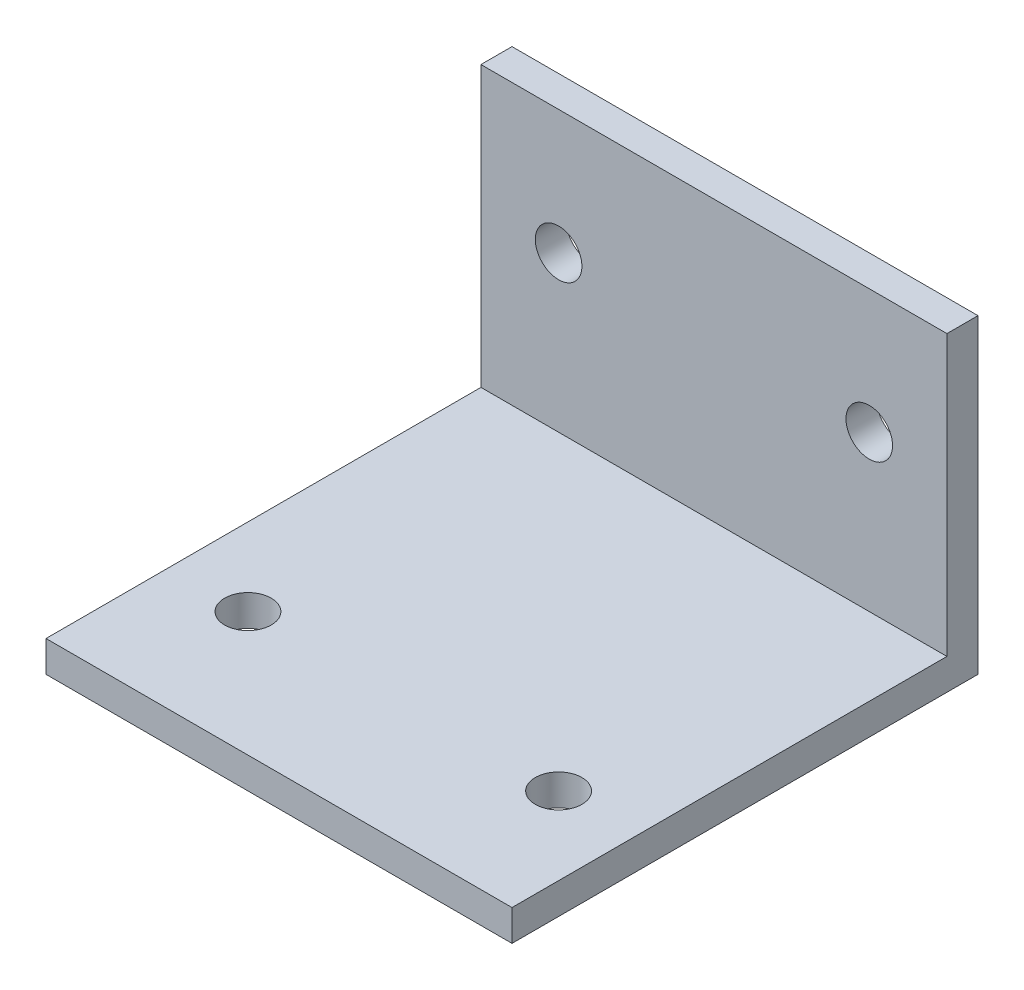
SolidWorks part; units mm, degrees
material "AISI 304"
ref_plane "前视基准面" through (0, 0, 0) normal (0, 0, 1) x (1, 0, 0)
ref_plane "上视基准面" through (0, 0, 0) normal (0, 1, 0) x (1, 0, 0)
ref_plane "右视基准面" through (0, 0, 0) normal (1, 0, 0) x (0, 0, -1)
sketch "草图1" plane through (0, 0, 0) normal (0, 0, 1) x (1, 0, 0)
  line L1 (-15, 19) -> (15, 19)
  line L2 (-15, 19) -> (-15, -19)
  line L3 (-15, -19) -> (15, -19)
  line L4 (15, 19) -> (15, -19)
  line L5 (-15, 19) -> (15, -19) construction
  line L6 (-15, -19) -> (15, 19) construction
  point P0 (0, 0)
  dimension "D1" = 30
  dimension "D2" = 38
extrude "凸台-拉伸1" add sketch "草图1" along normal blind 3
sketch "草图2" plane through (0, 0, 3) normal (0, 0, 1) x (1, 0, 0)
  line L0 (15, -19) -> (15, 19) construction
  line L1 (-15, -19) -> (15, -19)
  line L2 (-15, -19) -> (-15, -16)
  line L3 (-15, -16) -> (15, -16)
  line L4 (15, -19) -> (15, -16)
  dimension "D1" = 3
extrude "凸台-拉伸2" add sketch "草图2" along normal blind 35
sketch "草图3" plane through (0, 0, 3) normal (0, 0, 1) x (1, 0, 0)
  line L0 (15, -16) -> (15, 19) construction
  line L1 (-15, 19) -> (-15, -16) construction
  line L2 (15, 19) -> (-15, 19) construction
  circle A0 centre (-10, -6) radius 1.5
  circle A1 centre (10, -6) radius 1.5
  dimension "D1" = 3
  dimension "D2" = 3
  dimension "D3" = 5
  dimension "D4" = 5
  dimension "D5" = 25
  dimension "D6" = 25
extrude "切除-拉伸1" cut sketch "草图3" against normal blind 35
sketch "草图4" plane through (0, -16, 0) normal (0, 1, 0) x (1, 0, 0)
  line L1 (15, -38) -> (15, -3) construction
  line L2 (-15, -38) -> (-15, -3) construction
  line L3 (15, -38) -> (-15, -38) construction
  circle A0 centre (-10, -23) radius 1.5
  circle A1 centre (10, -23) radius 1.5
  dimension "D1" = 3
  dimension "D2" = 3
  dimension "D3" = 5
  dimension "D4" = 5
  dimension "D5" = 15
extrude "切除-拉伸2" cut sketch "草图4" against normal blind 35
sketch "草图5" plane through (0, -19, 0) normal (0, -1, 0) x (1, 0, 0)
  line L1 (-41.1883, 49.4744) -> (47.4485, 49.4744)
  line L2 (-41.1883, 49.4744) -> (-41.1883, -14.1195)
  line L3 (-41.1883, -14.1195) -> (47.4485, -14.1195)
  line L4 (47.4485, 49.4744) -> (47.4485, -14.1195)
extrude "切除-拉伸3" cut sketch "草图5" against normal blind 1
sketch "草图6" plane through (0, 0, 0) normal (0, 0, -1) x (-1, 0, 0)
  line L1 (25.7068, 22.7168) -> (-23.1859, 22.7168)
  line L2 (25.7068, 22.7168) -> (25.7068, -20.2152)
  line L3 (25.7068, -20.2152) -> (-23.1859, -20.2152)
  line L4 (-23.1859, 22.7168) -> (-23.1859, -20.2152)
extrude "切除-拉伸4" cut sketch "草图6" against normal blind 1
sketch "草图7" plane through (0, 0, 38) normal (0, 0, 1) x (1, 0, 0)
  line L1 (-19.0979, -12.7811) -> (17.213, -12.7811)
  line L2 (-19.0979, -12.7811) -> (-19.0979, -19.5205)
  line L3 (-19.0979, -19.5205) -> (17.213, -19.5205)
  line L4 (17.213, -12.7811) -> (17.213, -19.5205)
extrude "切除-拉伸5" cut sketch "草图7" against normal blind 7
sketch "草图8" plane through (0, 19, 0) normal (0, 1, 0) x (1, 0, 0)
  line L1 (19.2375, -7.3482) -> (-19.4018, -7.3482)
  line L2 (19.2375, -7.3482) -> (19.2375, 5.6096)
  line L3 (19.2375, 5.6096) -> (-19.4018, 5.6096)
  line L4 (-19.4018, -7.3482) -> (-19.4018, 5.6096)
extrude "切除-拉伸6" cut sketch "草图8" against normal blind 17
